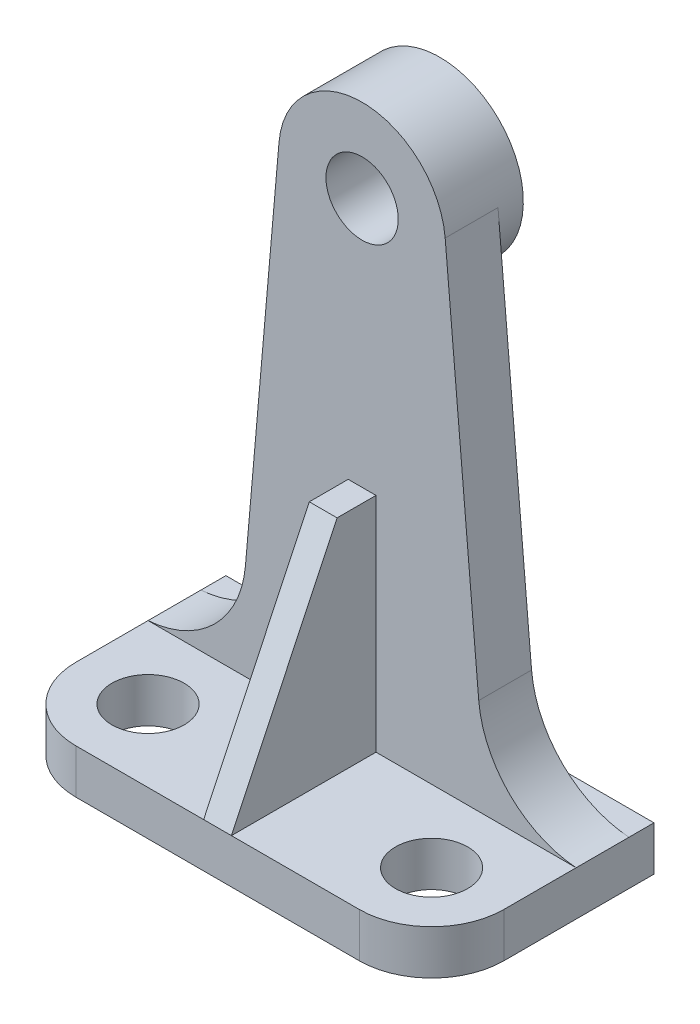
SolidWorks part; units mm, degrees
ref_plane "정면" through (0, 0, 0) normal (0, 0, 1) x (1, 0, 0)
ref_plane "윗면" through (0, 0, 0) normal (0, 1, 0) x (1, 0, 0)
ref_plane "우측면" through (0, 0, 0) normal (1, 0, 0) x (0, 0, -1)
sketch "스케치1" plane through (0, 0, 0) normal (0, 1, 0) x (1, 0, 0)
  line L1 (-38.5, 40) -> (38.5, 40)
  line L2 (-38.5, 40) -> (-38.5, 13)
  line L3 (-25.5, 0) -> (25.5, 0)
  line L4 (38.5, 40) -> (38.5, 13)
  line L5 (-38.5, 40) -> (38.5, 0) construction
  line L6 (-38.5, 0) -> (38.5, 40) construction
  arc A0 (-38.5, 13) -> (-25.5, 0) centre (-25.5, 13) ccw
  arc A1 (38.5, 13) -> (25.5, 0) centre (25.5, 13) cw
  point P0 (0, 20)
  dimension "D5" = 13
  dimension "D1" = 40
  dimension "D2" = 77
  dimension "D3" = 0
  dimension "D4" = 20
extrude "보스-돌출1" add sketch "스케치1" along normal blind 8
sketch "스케치2" plane through (0, 8, 0) normal (0, 1, 0) x (1, 0, 0)
  line L0 (0, 63.6865) -> (0, -19.2885) construction
  circle A0 centre (-25.5, 13) radius 6.5
  arc A1 (-38.5, 13) -> (-25.5, 0) centre (-25.5, 13) ccw construction
  circle A2 centre (25.5, 13) radius 6.5
  dimension "D1" = 13
extrude "컷-돌출1" cut sketch "스케치2" against normal blind 8
ref_plane "평면1" through (0, 0, -26) normal (0, 0, -1) x (-1, 0, 0)
sketch "스케치3" plane through (0, 0, -26) normal (0, 0, -1) x (-1, 0, 0)
  line L0 (-38.5, 0) -> (-38.5, 8)
  line L1 (-38.5, 0) -> (38.5, 0)
  line L2 (38.5, 0) -> (38.5, 8)
  line L3 (-38.5, 8) -> (38.5, 8) construction
  line L4 (-38.5, 8) -> (-38.5, 0) construction
  line L5 (-38.5, 0) -> (38.5, 0) construction
  line L6 (38.5, 8) -> (38.5, 0) construction
  line L7 (-14.9429, 94.3073) -> (-20.981, 25.2917)
  line L8 (14.9429, 94.3073) -> (20.981, 25.2917)
  arc A0 (-38.5, 8) -> (-20.981, 25.2917) centre (-39.9087, 26.9477) ccw
  arc A1 (38.5, 8) -> (20.981, 25.2917) centre (39.9087, 26.9477) cw
  arc A2 (14.9429, 94.3073) -> (-14.9429, 94.3073) centre (0, 93) ccw
  point P5 (0, 0)
  point P15 (0, 0)
  point P21 (0, 0)
  point P22 (7.1663, 92.7235)
  point P23 (0, 0)
  dimension "D3" = 19
  dimension "D4" = 19
  dimension "D7" = 30
  dimension "D1" = 8
  dimension "D2" = 8
  dimension "D5" = 93
  dimension "D6" = 0
  dimension "D8" = 85
  dimension "D9" = 85
extrude "보스-돌출2" add sketch "스케치3" along normal blind 9.5
sketch "스케치4" plane through (0, 0, -35.5) normal (0, 0, -1) x (-1, 0, 0)
  circle A0 centre (0, 93) radius 15
  arc A1 (14.9429, 94.3073) -> (-14.9429, 94.3073) centre (0, 93) ccw construction
extrude "보스-돌출3" add sketch "스케치4" along normal blind 4.5
sketch "스케치5" plane through (0, 0, -40) normal (0, 0, -1) x (-1, 0, 0)
  circle A0 centre (0, 93) radius 6.5
  circle A1 centre (0, 93) radius 15 construction
  dimension "D1" = 13
extrude "컷-돌출2" cut sketch "스케치5" against normal through all
sketch "스케치7" plane through (0, 0, 0) normal (1, 0, 0) x (0, 0, -1)
  line L0 (0, 8) -> (35.5, 8)
  line L1 (35.5, 8) -> (26, 8) construction
  line L2 (35.5, 8) -> (35.5, 48)
  line L3 (35.5, 25.2917) -> (35.5, 94.3073) construction
  line L4 (35.5, 48) -> (19, 48)
  line L5 (19, 48) -> (0, 8)
  line L6 (26, 25.2917) -> (26, 94.3073) construction
  dimension "D1" = 40
  dimension "D2" = 7
  dimension "D3" = 40
extrude "보스-돌출4" add sketch "스케치7" along normal mid plane 5
